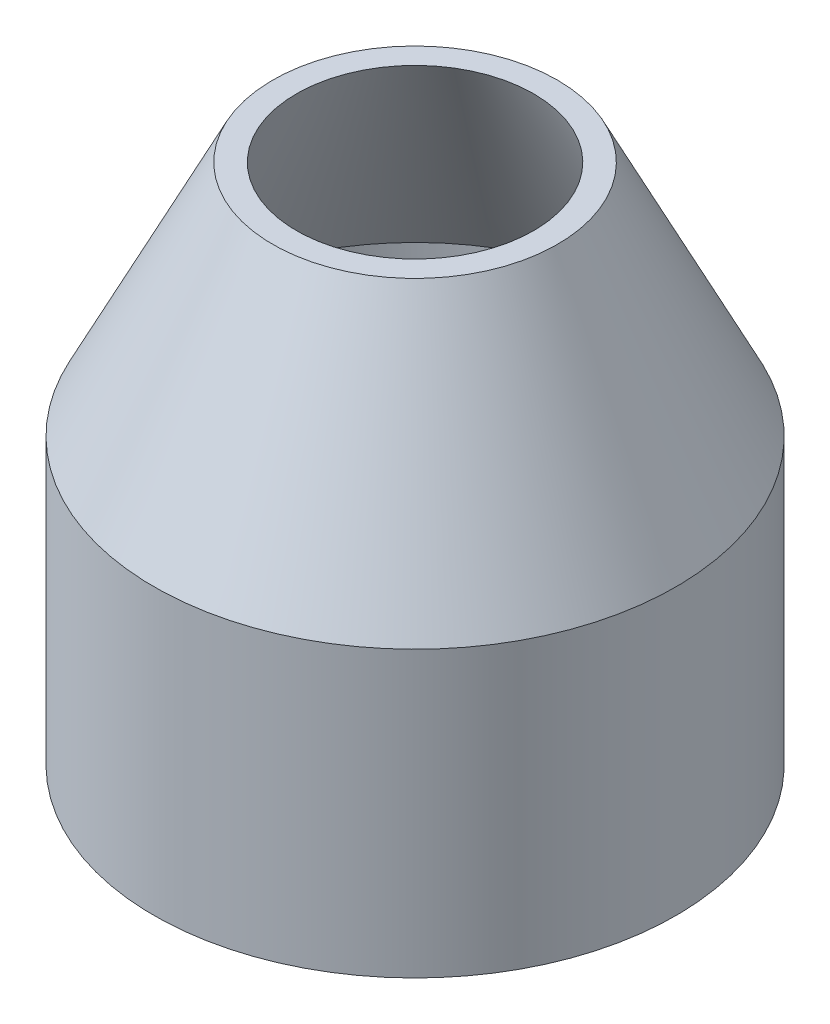
SolidWorks part; units mm, degrees
ref_plane "Front Plane" through (0, 0, 0) normal (0, 0, 1) x (1, 0, 0)
ref_plane "Top Plane" through (0, 0, 0) normal (0, 1, 0) x (1, 0, 0)
ref_plane "Right Plane" through (0, 0, 0) normal (1, 0, 0) x (0, 0, -1)
sketch "Sketch1" plane through (0, 0, 0) normal (0, 0, 1) x (1, 0, 0)
  line L0 (0, 0) -> (0, 60.8172) construction
  line L1 (5.5, 0) -> (5.5, 6)
  line L2 (5.5, 6) -> (3, 11)
  line L3 (3, 11) -> (2.5, 11)
  line L4 (2.5, 11) -> (5, 6)
  line L5 (5, 6) -> (5, 0)
  line L6 (5, 0) -> (5.5, 0)
  dimension "D1" = 0.5
  dimension "D2" = 11
  dimension "D4" = 5
  dimension "D5" = 6
revolve "Revolve2" add sketch "Sketch1" angle 360 about L0
